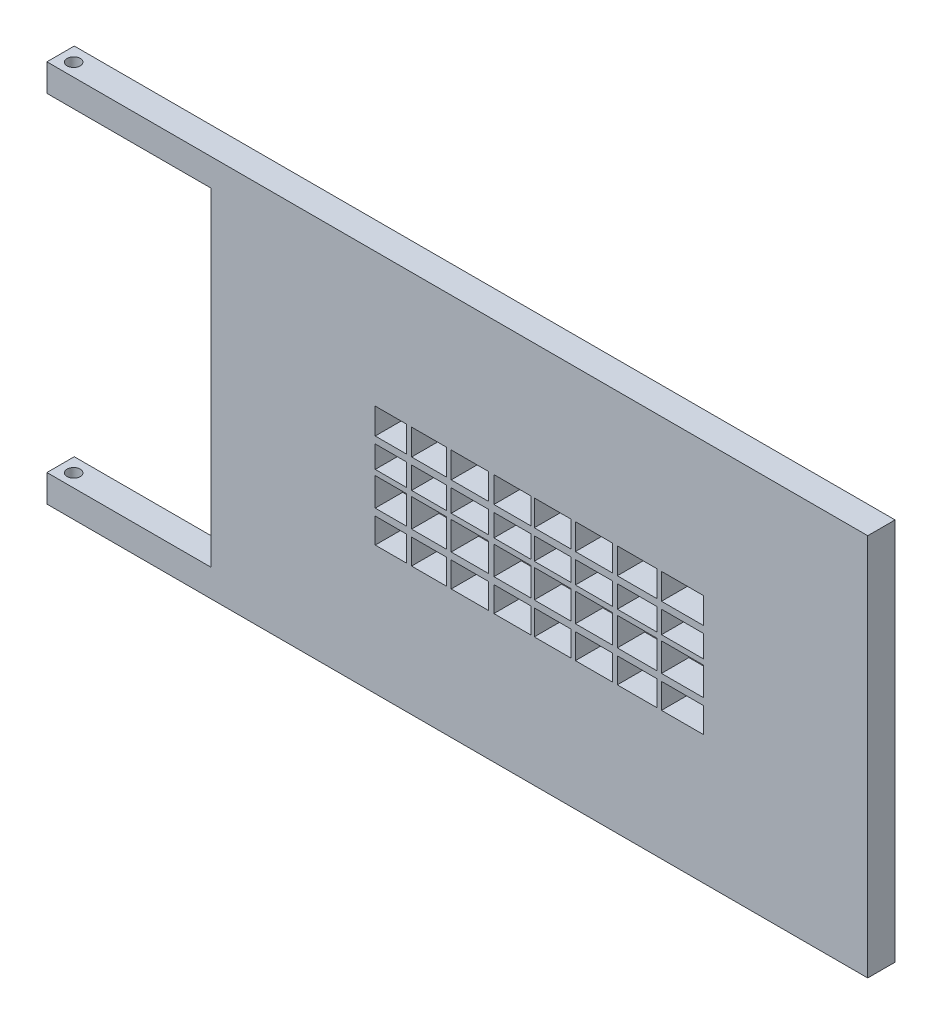
SolidWorks part; units mm, degrees
material "Beech"
ref_plane "Front Plane" through (0, 0, 0) normal (0, 0, 1) x (1, 0, 0)
ref_plane "Top Plane" through (0, 0, 0) normal (0, 1, 0) x (1, 0, 0)
ref_plane "Right Plane" through (0, 0, 0) normal (1, 0, 0) x (0, 0, -1)
sketch "Sketch1" plane through (0, 0, 0) normal (0, 0, 1) x (1, 0, 0)
  line L1 (0, 0) -> (600, 0)
  line L2 (0, 0) -> (0, 350)
  line L3 (0, 350) -> (600, 350)
  line L4 (600, 0) -> (600, 350)
  dimension "D1" = 600
  dimension "D2" = 350
extrude "Boss-Extrude1" add sketch "Sketch1" along normal blind 25
sketch "Sketch3" plane through (0, 0, 0) normal (-1, 0, 0) x (0, 0, 1)
  line L0 (0, 350) -> (0, 0) construction
  line L1 (0, 25) -> (25, 25)
  line L2 (0, 25) -> (0, 0)
  line L3 (0, 0) -> (25, 0)
  line L4 (25, 25) -> (25, 0)
  line L5 (25, 350) -> (25, 0) construction
  line L6 (0, 350) -> (25, 350)
  line L7 (0, 350) -> (0, 325)
  line L8 (0, 325) -> (25, 325)
  line L9 (25, 350) -> (25, 325)
  dimension "D1" = 25
  dimension "D2" = 25
extrude "Boss-Extrude2" add sketch "Sketch3" along normal blind 150
sketch "Sketch4" plane through (0, 0, 0) normal (0, -1, 0) x (1, 0, 0)
  circle A0 centre (-137.5, 13.055) radius 6
  dimension "D3" = 12
  dimension "D1" = 13.055
  dimension "D2" = 12.5
extrude "Cut-Extrude1" cut sketch "Sketch4" against normal blind 370
sketch "Sketch5" plane through (0, 0, 25) normal (0, 0, 1) x (1, 0, 0)
  line L1 (150, 227.57) -> (450, 227.57)
  line L2 (150, 227.57) -> (150, 117.57)
  line L3 (150, 117.57) -> (450, 117.57)
  line L4 (450, 227.57) -> (450, 117.57)
  line L5 (178.3599, 227.57) -> (183.2327, 227.57)
  line L6 (178.3599, 227.57) -> (178.3599, 117.57)
  line L7 (178.3599, 117.57) -> (183.2327, 117.57)
  line L8 (183.2327, 227.57) -> (183.2327, 117.57)
  line L9 (215.2543, 227.57) -> (219.431, 227.57)
  line L10 (215.2543, 227.57) -> (215.2543, 117.57)
  line L11 (215.2543, 117.57) -> (219.431, 117.57)
  line L12 (219.431, 227.57) -> (219.431, 117.57)
  line L13 (253.541, 227.57) -> (258.4138, 227.57)
  line L14 (253.541, 227.57) -> (253.541, 117.57)
  line L15 (253.541, 117.57) -> (258.4138, 117.57)
  line L16 (258.4138, 227.57) -> (258.4138, 117.57)
  line L17 (292.5238, 227.57) -> (295.3083, 227.57)
  line L18 (292.5238, 227.57) -> (292.5238, 117.57)
  line L19 (292.5238, 117.57) -> (295.3083, 117.57)
  line L20 (295.3083, 227.57) -> (295.3083, 117.57)
  line L21 (328.7221, 227.57) -> (332.8988, 227.57)
  line L22 (328.7221, 227.57) -> (328.7221, 117.57)
  line L23 (328.7221, 117.57) -> (332.8988, 117.57)
  line L24 (332.8988, 227.57) -> (332.8988, 117.57)
  line L25 (367.0087, 227.57) -> (371.1855, 227.57)
  line L26 (367.0087, 227.57) -> (367.0087, 117.57)
  line L27 (367.0087, 117.57) -> (371.1855, 117.57)
  line L28 (371.1855, 227.57) -> (371.1855, 117.57)
  line L29 (407.3838, 227.57) -> (411.5605, 227.57)
  line L30 (407.3838, 227.57) -> (407.3838, 117.57)
  line L31 (407.3838, 117.57) -> (411.5605, 117.57)
  line L32 (411.5605, 227.57) -> (411.5605, 117.57)
  line L33 (150, 203.889) -> (450, 203.889)
  line L34 (150, 203.889) -> (150, 197.6239)
  line L35 (150, 197.6239) -> (450, 197.6239)
  line L36 (450, 203.889) -> (450, 197.6239)
  line L37 (150, 172.57) -> (450, 172.57)
  line L38 (150, 172.57) -> (150, 177.4364)
  line L39 (150, 177.4364) -> (450, 177.4364)
  line L40 (450, 172.57) -> (450, 177.4364)
  line L41 (150, 146.8071) -> (450, 146.8071)
  line L42 (150, 146.8071) -> (150, 140.542)
  line L43 (150, 140.542) -> (450, 140.542)
  line L44 (450, 146.8071) -> (450, 140.542)
  dimension "D1" = 150
  dimension "D2" = 150
  dimension "D3" = 110
extrude "Cut-Extrude3" cut sketch "Sketch5" against normal blind 30 contours L2 L33 L6 L1 | L8 L33 L10 L1 | L12 L33 L14 L1 | L16 L33 L18 L1 | L20 L33 L22 L1 | L24 L33 L26 L1 | L28 L33 L30 L1 | L32 L33 L4 L1 | L2 L39 L6 L35 | L8 L39 L10 L35 | L12 L39 L14 L35 | L16 L39 L18 L35 | L20 L39 L22 L35 | L24 L39 L26 L35 | L28 L39 L30 L35 | L32 L39 L4 L35 | L32 L41 L4 L37 | L28 L41 L30 L37 | L24 L41 L26 L37 | L20 L41 L22 L37 | L16 L41 L18 L37 | L12 L41 L14 L37 | L8 L41 L10 L37 | L2 L41 L6 L37 | L43 L2 L3 L6 | L43 L8 L3 L10 | L43 L12 L3 L14 | L43 L16 L3 L18 | L43 L20 L3 L22 | L43 L24 L3 L26 | L43 L28 L3 L30 | L43 L32 L3 L4
sketch "Sketch7" plane through (0, 0, 0) normal (0, 0, -1) x (-1, 0, 0)
  line L1 (-551.4809, 285.3352) -> (-540.4809, 285.3352)
  line L2 (-551.4809, 285.3352) -> (-551.4809, 72.3221)
  line L3 (-551.4809, 72.3221) -> (-540.4809, 72.3221)
  line L4 (-540.4809, 285.3352) -> (-540.4809, 72.3221)
extrude "Boss-Extrude4" add sketch "Sketch7" along normal blind 30
sketch "Sketch8" plane through (0, 0, 0) normal (0, 0, -1) x (-1, 0, 0)
  line L1 (-551.4809, 291.6003) -> (-510.4097, 291.6003)
  line L2 (-551.4809, 291.6003) -> (-551.4809, 285.3352)
  line L3 (-551.4809, 285.3352) -> (-510.4097, 285.3352)
  line L4 (-510.4097, 291.6003) -> (-510.4097, 285.3352)
  line L5 (-551.4809, 72.3221) -> (-510.4097, 72.3221)
  line L6 (-551.4809, 72.3221) -> (-551.4809, 66.057)
  line L7 (-551.4809, 66.057) -> (-510.4097, 66.057)
  line L8 (-510.4097, 72.3221) -> (-510.4097, 66.057)
extrude "Boss-Extrude5" add sketch "Sketch8" along normal blind 30
sketch "Sketch10" plane through (0, 72.3221, 0) normal (0, 1, 0) x (1, 0, 0)
  circle A0 centre (529.8662, 14.7061) radius 8
  dimension "D1" = 16
sketch "Sketch11" plane through (0, 285.3352, 0) normal (0, -1, 0) x (1, 0, 0)
  circle A0 centre (528.1391, -14.1943) radius 8
  dimension "D1" = 16
extrude "Cut-Extrude6" cut sketch "Sketch11" against normal blind 4 and the other way blind 217
